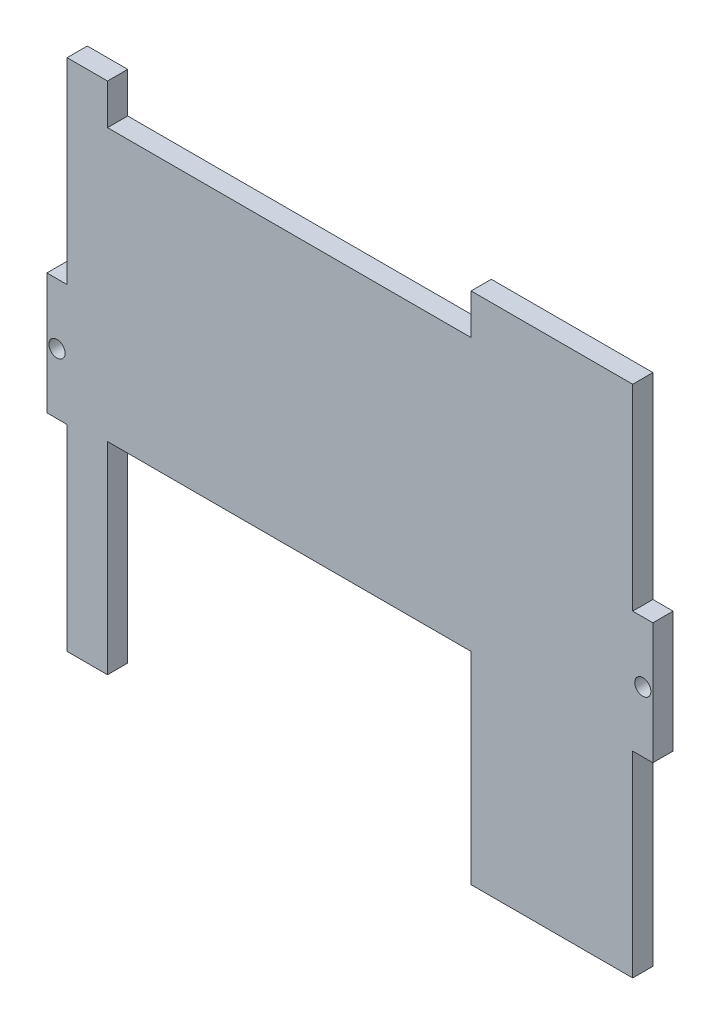
SolidWorks part; units mm, degrees
ref_plane "Front Plane" through (0, 0, 0) normal (0, 0, 1) x (1, 0, 0)
ref_plane "Top Plane" through (0, 0, 0) normal (0, 1, 0) x (1, 0, 0)
ref_plane "Right Plane" through (0, 0, 0) normal (1, 0, 0) x (0, 0, -1)
sketch "Sketch1" plane through (0, 0, 0) normal (0, 0, 1) x (1, 0, 0)
  line L0 (0, 63.64) -> (0, -63.64) construction
  line L1 (-70, -63.64) -> (75, -63.64)
  line L2 (-75, -15) -> (-75, 15)
  line L3 (-70, 63.64) -> (70, 63.64)
  line L4 (75, -15) -> (75, 15)
  line L5 (-70, -59.3973) -> (70, 59.3973) construction
  line L6 (-70, 59.3973) -> (75, -63.64) construction
  line L7 (-70, 63.64) -> (-70, 15)
  line L8 (70, 63.64) -> (70, 15)
  line L9 (-75, 0) -> (75, 0) construction
  line L10 (-75, -15) -> (-70, -15)
  line L11 (-75, 15) -> (-70, 15)
  line L12 (-70, -15) -> (-70, -63.64)
  line L13 (70, -15) -> (70, -63.64)
  line L14 (-70, 63.64) -> (-70, -63.64) construction
  line L15 (70, 15) -> (75, 15)
  line L16 (70, 63.64) -> (70, -63.64) construction
  line L17 (70, -15) -> (75, -15)
  line L18 (-75, 15) -> (75, 15) construction
  line L20 (-75, -15) -> (75, -15) construction
  point P0 (0, 0)
  dimension "D3" = 70
  dimension "D5" = 15
  dimension "D4" = 70
  dimension "D6" = 15
extrude "Boss-Extrude1" add sketch "Sketch1" along normal blind 5 contours L13 L17 L4 L15 L8 L3 L7 L11 L2 L10 L12 L1
sketch "Sketch2" plane through (0, 0, 5) normal (0, 0, 1) x (1, 0, 0)
  line L0 (-75, 15) -> (-70, 15) construction
  line L1 (-75, -15) -> (-70, -15) construction
  line L2 (-72.5, 15) -> (-72.5, -15) construction
  line L3 (0, 63.64) -> (0, -63.64) construction
  line L4 (-70, 63.64) -> (70, 63.64) construction
  line L5 (-70, -63.64) -> (70, -63.64) construction
  circle A0 centre (-72.5, 0) radius 2
  circle A1 centre (72.5, 0) radius 2
  dimension "D1" = 4
extrude "Cut-Extrude1" cut sketch "Sketch2" against normal blind 5
sketch "Sketch3" plane through (0, 0, 5) normal (0, 0, 1) x (1, 0, 0)
  line L0 (-70, 63.64) -> (70, 63.64) construction
  line L1 (30, 53.64) -> (-60, 53.64)
  line L2 (30, 53.64) -> (30, 63.64)
  line L3 (30, 63.64) -> (-60, 63.64)
  line L4 (-60, 53.64) -> (-60, 63.64)
  line L5 (30, 53.64) -> (-60, 63.64) construction
  line L6 (30, 63.64) -> (-60, 53.64) construction
  line L7 (-76.5013, 0) -> (74.5, 0) construction
  line L8 (30, -63.64) -> (-60, -13.64) construction
  line L9 (30, -13.64) -> (-60, -63.64) construction
  line L10 (-60, -13.64) -> (-60, -63.64)
  line L11 (30, -63.64) -> (-60, -63.64)
  line L12 (30, -13.64) -> (30, -63.64)
  line L13 (30, -13.64) -> (-60, -13.64)
  circle A0 centre (72.5, 0) radius 2 construction
  point P0 (-15, 58.64)
  point P17 (-15, -38.64)
  dimension "D1" = 10
  dimension "D2" = 90
  dimension "D3" = 15
  dimension "D4" = 50
  dimension "D5" = 90
extrude "Cut-Extrude2" cut sketch "Sketch3" against normal blind 5
